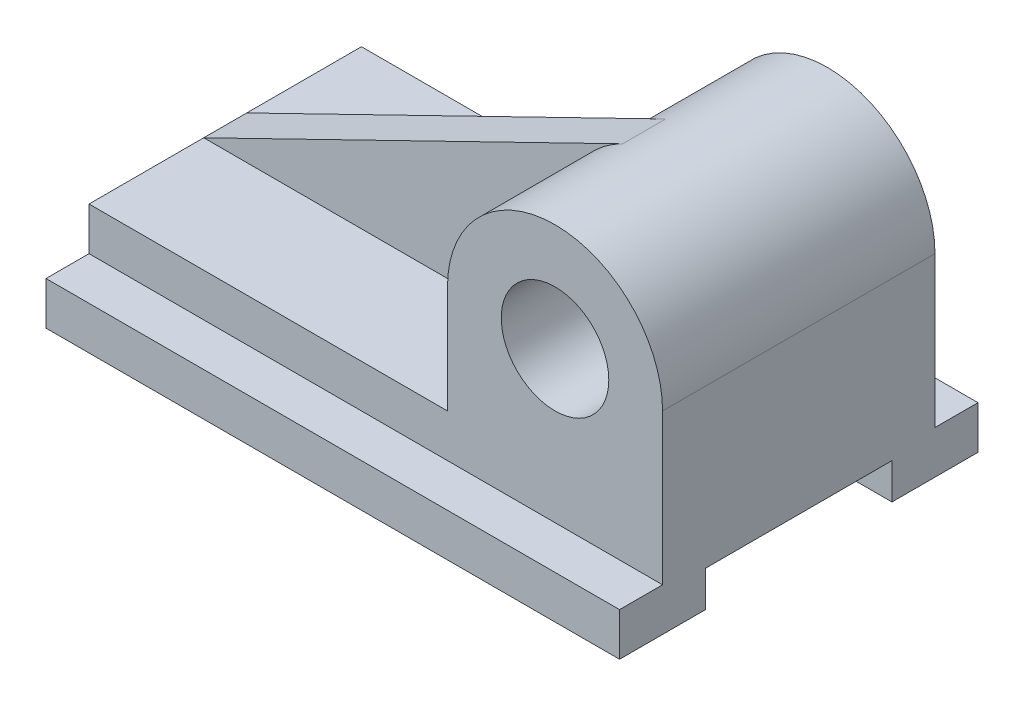
SolidWorks part; units mm, degrees
ref_plane "Front Plane" through (0, 0, 0) normal (0, 0, 1) x (1, 0, 0)
ref_plane "Top Plane" through (0, 0, 0) normal (0, 1, 0) x (1, 0, 0)
ref_plane "Right Plane" through (0, 0, 0) normal (1, 0, 0) x (0, 0, -1)
sketch "Sketch1" plane through (0, 0, 0) normal (0, 0, 1) x (1, 0, 0)
  line L1 (-80, 12) -> (80, 12)
  line L2 (-80, 12) -> (-80, -12)
  line L3 (-80, -12) -> (80, -12)
  line L4 (80, 12) -> (80, -12)
  line L5 (-80, 12) -> (80, -12) construction
  line L6 (-80, -12) -> (80, 12) construction
  line L7 (80, 12) -> (20, 12)
  line L8 (80, 12) -> (80, 42)
  line L10 (20, 12) -> (20, 42)
  arc A0 (80, 42) -> (20, 42) centre (50, 42) ccw
  point P0 (0, 0)
  dimension "D1" = 160
  dimension "D2" = 24
  dimension "D3" = 30
  dimension "D4" = 60
extrude "Boss-Extrude1" add sketch "Sketch1" against normal blind 76 contours L4 L1 L2 L3 | L8 A0 L10 L1
ref_plane "Plane1" through (0, 0, -32) normal (0, 0, 1) x (1, 0, 0)
sketch "Sketch2" plane through (0, 0, -32) normal (0, 0, 1) x (1, 0, 0)
  line L0 (-80, 12) -> (36.8539, 68.9663)
  line L1 (-80, 12) -> (20, 12)
  line L2 (20, 12) -> (20, 42)
  arc A0 (36.8539, 68.9663) -> (20, 42) centre (50, 42) ccw
extrude "Boss-Extrude2" add sketch "Sketch2" against normal blind 12 contours A0 L2 L1 L0
sketch "Sketch3" plane through (0, 0, 0) normal (0, 0, 1) x (1, 0, 0)
  circle A0 centre (50, 42) radius 15
extrude "Cut-Extrude1" cut sketch "Sketch3" against normal blind 95 contours A0
sketch "Sketch4" plane through (-80, 0, 0) normal (-1, 0, 0) x (0, 0, 1)
  line L0 (-38, -12) -> (-12, -12)
  line L1 (-76, -12) -> (0, -12) construction
  line L2 (-12, -12) -> (-12, -2)
  line L3 (-12, -2) -> (-64, -2)
  line L4 (-64, -2) -> (-64, -12)
  line L5 (-64, -12) -> (-38, -12)
extrude "Cut-Extrude2" cut sketch "Sketch4" against normal blind 196
sketch "Sketch5" plane through (0, 0, 0) normal (0, 0, 1) x (1, 0, 0)
  line L0 (80, 42) -> (80, -12) construction
  line L1 (-80, -12) -> (80, -12)
  line L2 (-80, -12) -> (-80, 0)
  line L3 (-80, 0) -> (80, 0)
  line L4 (80, -12) -> (80, 0)
  dimension "D1" = 12
extrude "Boss-Extrude3" add sketch "Sketch5" along normal blind 12
sketch "Sketch6" plane through (0, 0, -76) normal (0, 0, -1) x (-1, 0, 0)
  line L0 (80, 12) -> (80, -12) construction
  line L1 (-80, -12) -> (80, -12)
  line L2 (-80, -12) -> (-80, 0)
  line L3 (-80, 0) -> (80, 0)
  line L4 (80, -12) -> (80, 0)
extrude "Boss-Extrude4" add sketch "Sketch6" along normal blind 12
